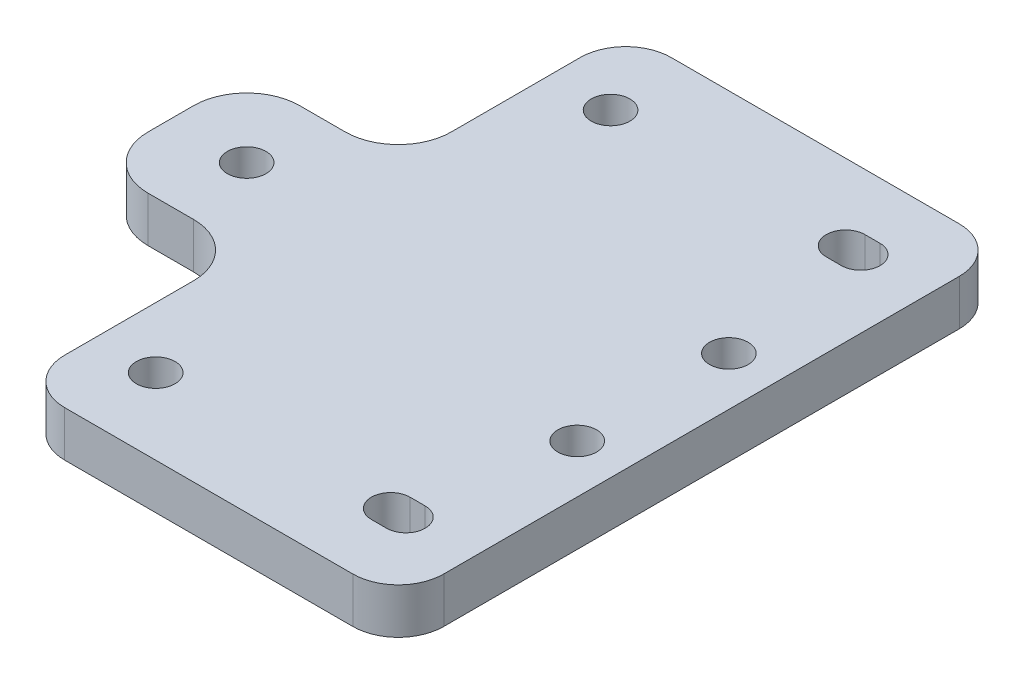
SolidWorks part; units mm, degrees
material "Клен"
ref_plane "Спереди" through (0, 0, 0) normal (0, 0, 1) x (1, 0, 0)
ref_plane "Сверху" through (0, 0, 0) normal (0, 1, 0) x (1, 0, 0)
ref_plane "Справа" through (0, 0, 0) normal (1, 0, 0) x (0, 0, -1)
sketch "Эскиз1" plane through (0, 0, 0) normal (0, 1, 0) x (1, 0, 0)
  line L0 (-56.8562, 0) -> (56.8562, 0) construction
  line L9 (-32, -10) -> (-38, -10)
  line L10 (-19, -40) -> (19, -40)
  line L11 (-25, -34) -> (-25, -17)
  line L12 (-19, 40) -> (19, 40)
  line L13 (25, -34) -> (25, 34)
  line L14 (-25, -40) -> (25, 40) construction
  line L15 (-25, 40) -> (25, -40) construction
  line L20 (-45, -3) -> (-45, 3)
  line L21 (-32, 10) -> (-38, 10)
  line L22 (-25, 17) -> (-25, 34)
  line L25 (-45, -10) -> (-25, 10) construction
  line L26 (-25, -10) -> (-72.5248, 37.5248) construction
  line L27 (-49, -29.3961) -> (-49, 34.1878) construction
  line L28 (440.105, 10) -> (12.105, 10) construction
  line L29 (12.105, 10.6243) -> (12.105, 12.7157) construction
  line L30 (440.105, 20) -> (12.105, 20) construction
  arc A4 (19, 40) -> (25, 34) centre (19, 34) cw
  arc A5 (19, -40) -> (25, -34) centre (19, -34) ccw
  arc A6 (-19, -40) -> (-25, -34) centre (-19, -34) cw
  arc A7 (-25, 34) -> (-19, 40) centre (-19, 34) cw
  circle A8 centre (-35, 0) radius 2.55
  arc A13 (-25, -17) -> (-32, -10) centre (-32, -17) ccw
  arc A14 (-32, 10) -> (-25, 17) centre (-32, 17) ccw
  arc A15 (-45, 3) -> (-38, 10) centre (-38, 3) cw
  arc A16 (-38, -10) -> (-45, -3) centre (-38, -3) cw
  circle A17 centre (18.605, 10) radius 2.55
  circle A18 centre (18.605, -10) radius 2.55
  point P0 (0, 0)
  point P22 (-45, -10)
  point P24 (-45, 10)
  point P25 (-75, 0)
  point P32 (-35, 0)
  point P34 (-49.8171, 0.0009)
  point P35 (-35, 0)
  point P36 (-24.7404, 0.0009)
  point P37 (-35, 0)
  point P39 (-35, 0)
  point P56 (-25, 25.5)
  dimension "D1" = 6
  dimension "D6" = 5.1
  dimension "D13" = 7
  dimension "D14" = 7
  dimension "D7" = 7
  dimension "D8" = 7
  dimension "D9" = 5.1
  dimension "D2" = 80
  dimension "D3" = 50
  dimension "D4" = 20
  dimension "D5" = 20
  dimension "D10" = 6.5
  dimension "D11" = 10
extrude "Бобышка-Вытянуть1" add sketch "Эскиз1" along normal blind 6
sketch "Эскиз2" plane through (0, 0, 0) normal (0, -1, 0) x (1, 0, 0)
  line L0 (0, -37.0349) -> (0, 29.2907) construction
  line L1 (16, -30) -> (14, -30) construction
  line L2 (16, -32.55) -> (14, -32.55)
  line L3 (16, -27.45) -> (14, -27.45)
  line L6 (-46.1924, 0) -> (55.6646, 0) construction
  line L7 (16, 30) -> (14, 30) construction
  line L8 (16, 32.55) -> (14, 32.55)
  line L9 (16, 27.45) -> (14, 27.45)
  line L10 (-25, 17) -> (-25, 34) construction
  line L11 (19, -40) -> (-19, -40) construction
  circle A0 centre (-17, -30) radius 2.55
  arc A1 (16, -32.55) -> (16, -27.45) centre (16, -30) ccw
  arc A2 (14, -27.45) -> (14, -32.55) centre (14, -30) ccw
  arc A3 (16, 32.55) -> (16, 27.45) centre (16, 30) cw
  arc A4 (14, 27.45) -> (14, 32.55) centre (14, 30) cw
  circle A5 centre (-17, 30) radius 2.55
  point P7 (15, -30)
  point P12 (15, -32.55)
  point P21 (15, 30)
  dimension "D1" = 5.1
  dimension "D2" = 5.1
  dimension "D3" = 2
  dimension "D4" = 33
  dimension "D5" = 8
  dimension "D6" = 10
extrude "Вырез-Вытянуть1" cut sketch "Эскиз2" against normal through all
equation "\"D2@Эскиз2\"=\"D1@Эскиз2\""
equation "\"D5@Эскиз1\"=\"D4@Эскиз1\""
